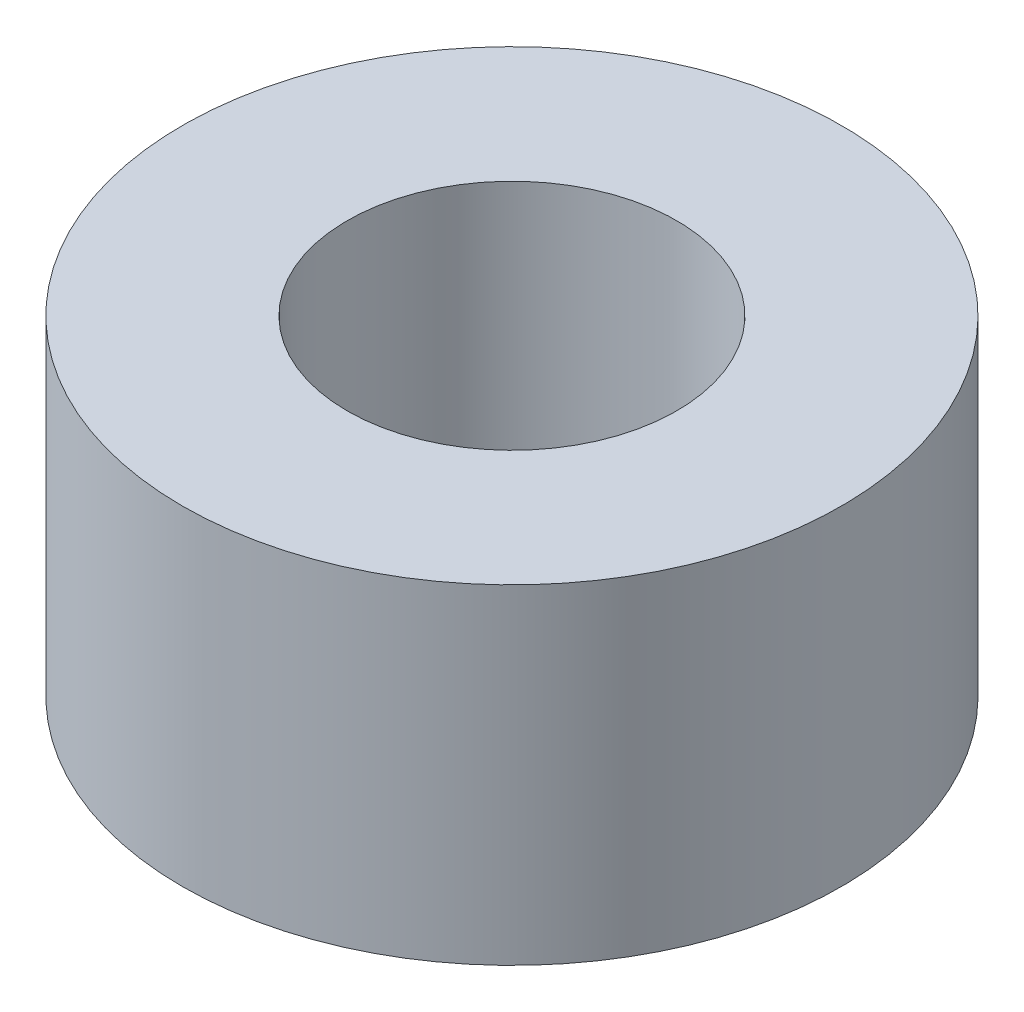
SolidWorks part; units mm, degrees
ref_plane "Front Plane" through (0, 0, 0) normal (0, 0, 1) x (1, 0, 0)
ref_plane "Top Plane" through (0, 0, 0) normal (0, 1, 0) x (1, 0, 0)
ref_plane "Right Plane" through (0, 0, 0) normal (1, 0, 0) x (0, 0, -1)
sketch "Sketch1" plane through (0, 0, 0) normal (0, 1, 0) x (1, 0, 0)
  circle A0 centre (0, 0) radius 5
  dimension "D1" = 10
extrude "Boss-Extrude1" add sketch "Sketch1" along normal blind 5
sketch "Sketch2" plane through (0, 5, 0) normal (0, 1, 0) x (1, 0, 0)
  circle A0 centre (0, 0) radius 2.5
  dimension "D1" = 5
extrude "Cut-Extrude1" cut sketch "Sketch2" against normal through all
